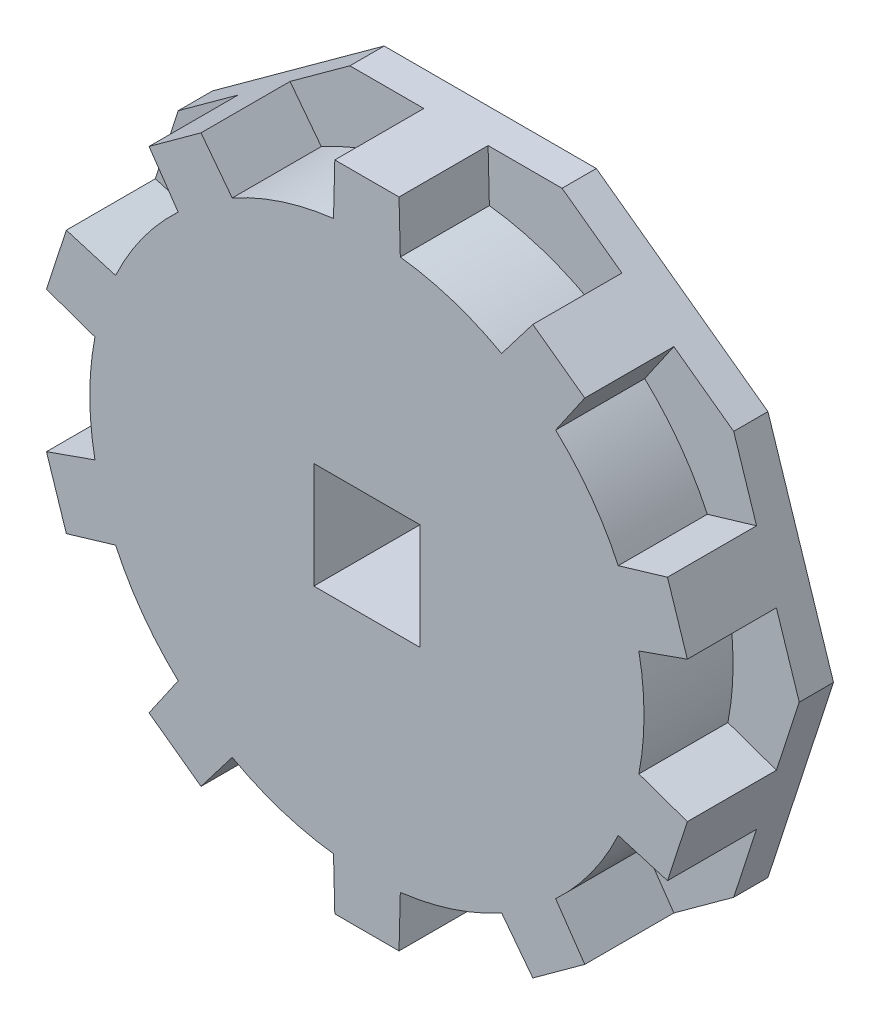
SolidWorks part; units mm, degrees
other "Marquage1"
sketch "Esquisse3" plane through (-18.5817, -19.0615, 0) normal (0, 0, -1) x (-1, 0, 0)
ref_plane "Plan de face" through (0, 0, 0) normal (0, 0, 1) x (1, 0, 0)
ref_plane "Plan de dessus" through (0, 0, 0) normal (0, 1, 0) x (1, 0, 0)
ref_plane "Plan de droite" through (0, 0, 0) normal (1, 0, 0) x (0, 0, -1)
sketch "Esquisse1" plane through (0, 0, 0) normal (0, 0, 1) x (1, 0, 0)
  line L0 (-5, 15.3884) -> (0, 0)
  line L2 (-1.95, 16.0624) -> (-1.875, 19.0615)
  line L3 (-1.875, 19.0615) -> (1.875, 19.0615)
  line L4 (1.95, 16.0624) -> (1.875, 19.0615)
  line L5 (0, 0) -> (5, 15.3884)
  line L6 (0, 0) -> (0, 83.6819) construction
  arc A1 (-5, 15.3884) -> (-1.95, 16.0624) centre (0, 0) cw
  arc A2 (1.95, 16.0624) -> (5, 15.3884) centre (0, 0) cw
  dimension "D2" = 10
  dimension "D3" = 3
  dimension "D1" = 36
  dimension "D4" = 3.75
  dimension "D5" = 3.9
extrude "Boss.-Extru.1" add sketch "Esquisse1" along normal blind 5.2
sketch "Esquisse4" plane through (0, 0, 0) normal (0, 0, -1) x (-1, 0, 0)
  line L0 (0, 0) -> (-6.1934, 19.0615)
  line L1 (-6.1934, 19.0615) -> (6.1934, 19.0615)
  line L2 (6.1934, 19.0615) -> (0, 0)
  line L3 (0, 0) -> (-5, 15.3884) construction
  line L4 (5, 15.3884) -> (0, 0) construction
  line L5 (-1.875, 19.0615) -> (1.875, 19.0615) construction
extrude "Boss.-Extru.2" add sketch "Esquisse4" along normal blind 2
fillet "Congé1" [suppressed] radius 0.5
pattern_circular "Répétition circulaire1" count 10 over 360 about axis through (0, 0, 0) along (0, 0, 1) of "Boss.-Extru.1", "Boss.-Extru.2"
sketch "Esquisse2" plane through (0, 0, 5.2) normal (0, 0, 1) x (1, 0, 0)
  line L1 (-3.1, -3.1) -> (3.1, -3.1)
  line L2 (-3.1, -3.1) -> (-3.1, 3.1)
  line L3 (-3.1, 3.1) -> (3.1, 3.1)
  line L4 (3.1, -3.1) -> (3.1, 3.1)
  line L5 (-3.1, -3.1) -> (3.1, 3.1) construction
  line L6 (-3.1, 3.1) -> (3.1, -3.1) construction
  point P0 (0, 0)
  point P6 (2.641, -0.2533)
  point P7 (-0.725, -3.7895)
  dimension "D1" = 6.2
extrude "Enlèv. mat.-Extru.1" cut sketch "Esquisse2" against normal through all
chamfer "Chanfrein1" [suppressed] distance 0.5 angle 45
